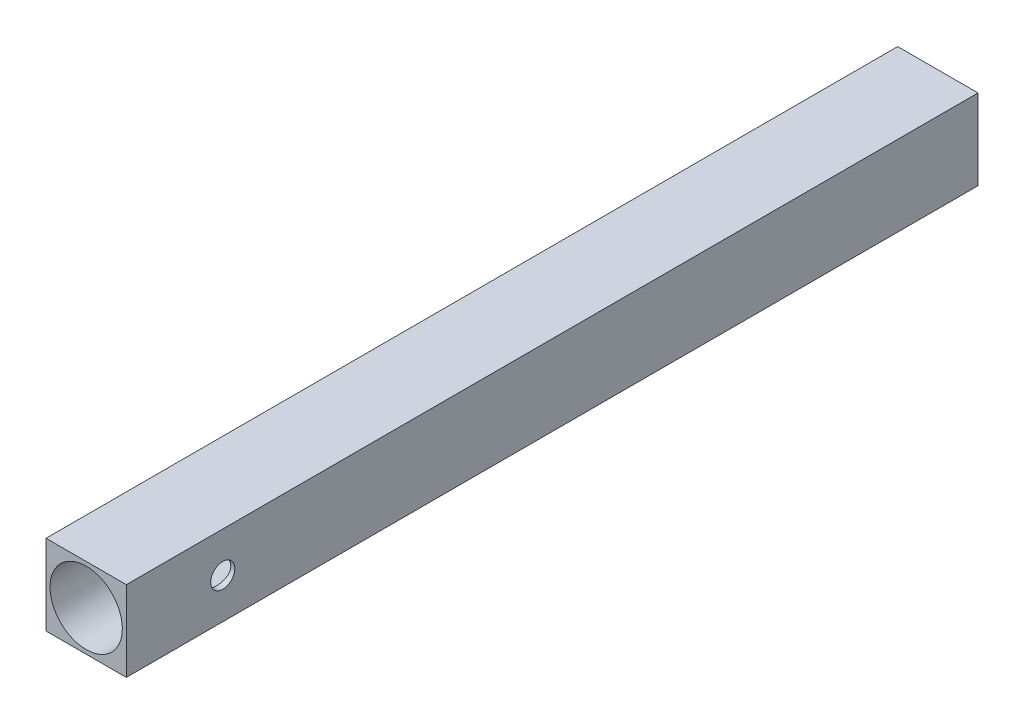
SolidWorks part; units mm, degrees
ref_plane "Front" through (0, 0, 0) normal (0, 0, 1) x (1, 0, 0)
ref_plane "Top" through (0, 0, 0) normal (0, 1, 0) x (1, 0, 0)
ref_plane "Right" through (0, 0, 0) normal (1, 0, 0) x (0, 0, -1)
sketch "草图1" plane through (0, 0, 0) normal (0, 0, 1) x (1, 0, 0)
  line L0 (-12.96, 0) -> (0, 0) construction
  line L1 (0, 0) -> (0, 14.208) construction
  line L3 (-10, 10) -> (10, 10)
  line L4 (-10, 10) -> (-10, -10)
  line L5 (-10, -10) -> (10, -10)
  line L6 (10, 10) -> (10, -10)
  circle A0 centre (0, 0) radius 9
  dimension "D1" = 20
  dimension "D2" = 20
  dimension "D3" = 10
  dimension "D4" = 10
extrude "凸台-拉伸1" add sketch "草图1" along normal blind 190
sketch "草图2" plane through (0, 0, 0) normal (0, 0, -1) x (-1, 0, 0)
  line L1 (10, 10) -> (-10, 10)
  line L2 (10, 10) -> (10, -10)
  line L3 (10, -10) -> (-10, -10)
  line L4 (-10, 10) -> (-10, -10)
extrude "凸台-拉伸2" add sketch "草图2" along normal blind 22
sketch "草图4" plane through (10, 0, 0) normal (1, 0, 0) x (0, 0, -1)
  line L0 (-190, -10) -> (-190, 10) construction
  circle A0 centre (-166, 0) radius 3
  dimension "D1" = 24
extrude "切除-拉伸2" cut sketch "草图4" against normal blind 10
